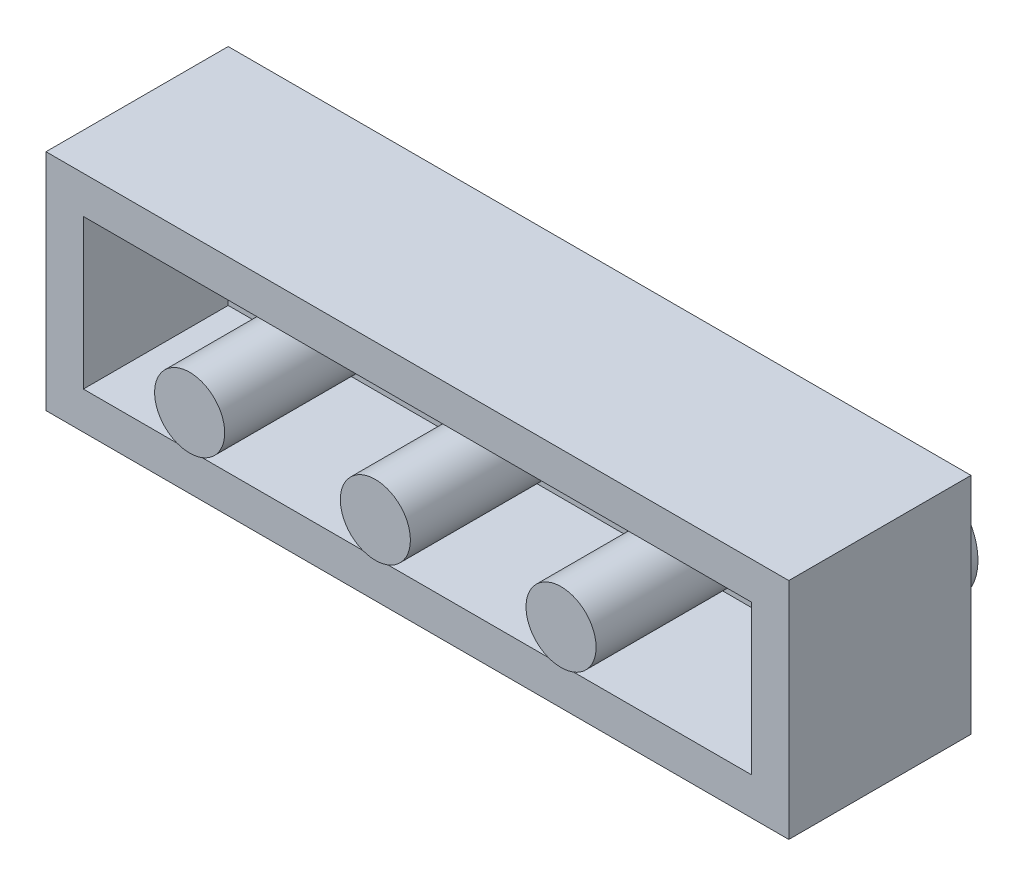
SolidWorks part; units mm, degrees
ref_plane "Front Plane" through (0, 0, 0) normal (0, 0, 1) x (1, 0, 0)
ref_plane "Top Plane" through (0, 0, 0) normal (0, 1, 0) x (1, 0, 0)
ref_plane "Right Plane" through (0, 0, 0) normal (1, 0, 0) x (0, 0, -1)
sketch "Sketch1" plane through (0, 0, 0) normal (0, 1, 0) x (1, 0, 0)
  line L1 (-15.9, 3.9) -> (15.9, 3.9)
  line L2 (-15.9, 3.9) -> (-15.9, -3.9)
  line L3 (-15.9, -3.9) -> (15.9, -3.9)
  line L4 (15.9, 3.9) -> (15.9, -3.9)
  line L5 (-15.9, 3.9) -> (15.9, -3.9) construction
  line L6 (-15.9, -3.9) -> (15.9, 3.9) construction
  point P0 (0, 0)
  dimension "D1" = 31.8
  dimension "D2" = 7.8
extrude "Boss-Extrude1" add sketch "Sketch1" along normal mid plane 9.6
shell "Shell2" thickness 1.6
sketch "Sketch2" plane through (0, 0, -3.9) normal (0, 0, -1) x (-1, 0, 0)
  line L0 (15.9, 4.8) -> (15.9, -4.8) construction
  circle A0 centre (12, 0) radius 2.4
  dimension "D2" = 4.8
  dimension "D1" = 3.9
extrude "Boss-Extrude2" add sketch "Sketch2" along normal blind 1.8
pattern_linear "LPattern1" count 6 spacing 8 along (1, 0, 0) of "Boss-Extrude2"
sketch "Sketch3" plane through (0, 0, -2.3) normal (0, 0, 1) x (1, 0, 0)
  line L0 (-15.9, 4.8) -> (-15.9, -4.8) construction
  circle A0 centre (-7.95, 0) radius 1.5
  dimension "D2" = 3
  dimension "D1" = 7.95
extrude "Boss-Extrude3" add sketch "Sketch3" along normal blind 8
pattern_linear "LPattern2" count 3 spacing 7.95 along (1, 0, 0) of "Boss-Extrude3"
